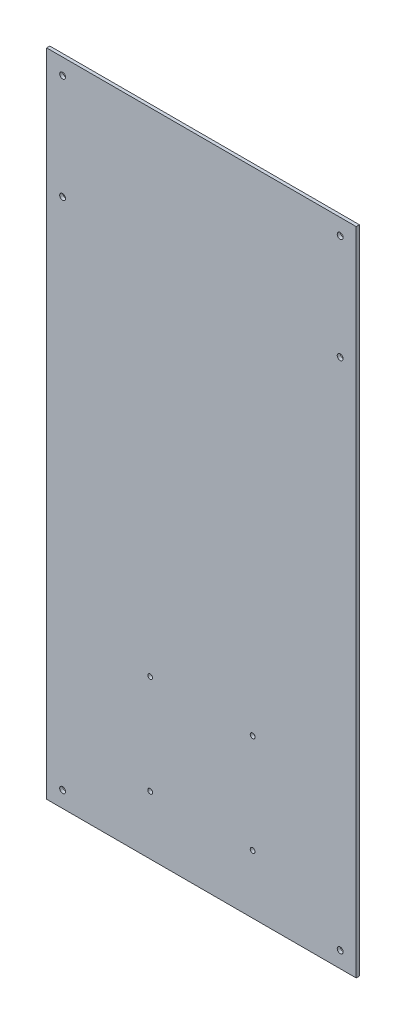
SolidWorks part; units mm, degrees
material "Acrylic (Medium-high impact)"
ref_plane "Front Plane" through (0, 0, 0) normal (0, 0, 1) x (1, 0, 0)
ref_plane "Top Plane" through (0, 0, 0) normal (0, 1, 0) x (1, 0, 0)
ref_plane "Right Plane" through (0, 0, 0) normal (1, 0, 0) x (0, 0, -1)
sketch "Sketch1" plane through (0, 0, 0) normal (0, 0, 1) x (1, 0, 0)
  line L0 (55, 0) -> (-55, 0) construction
  line L1 (-145, 304.8) -> (145, 304.8)
  line L2 (-145, 304.8) -> (-145, -304.8)
  line L3 (-145, -304.8) -> (145, -304.8)
  line L4 (145, 304.8) -> (145, -304.8)
  line L5 (-145, 304.8) -> (145, -304.8) construction
  line L6 (-145, -304.8) -> (145, 304.8) construction
  line L7 (48, -156.8) -> (-48, -249.8) construction
  line L8 (-48, -249.8) -> (48, -249.8) construction
  line L9 (48, -249.8) -> (48, -156.8) construction
  line L10 (48, -156.8) -> (-48, -156.8) construction
  line L11 (-48, -156.8) -> (-48, -249.8) construction
  line L12 (-48, -156.8) -> (48, -249.8) construction
  point P0 (0, 0)
  point P5 (-129.995, 289.795)
  point P6 (129.995, 289.795)
  point P7 (-48, -249.8)
  point P9 (-48, -156.8)
  point P10 (48, -156.8)
  point P11 (48, -249.8)
  point P12 (0, -203.3)
  point P16 (129.995, -289.795)
  point P17 (-129.995, -289.795)
  point P21 (-129.995, 191.395)
  point P22 (129.995, 191.395)
  point P23 (0, 0)
  point P24 (0, 0)
  point P25 (129.995, 191.395)
  point P26 (0, 0)
  point P27 (0, 0)
  dimension "D1" = 609.6
  dimension "D2" = 290
  dimension "D3" = 15.005
  dimension "D4" = 15.005
  dimension "D5" = 15.005
  dimension "D6" = 93
  dimension "D7" = 96
  dimension "D8" = 55
  dimension "D9" = 98.4
extrude "Boss-Extrude1" add sketch "Sketch1" along normal blind 3
hole_wizard "M5 Clearance Hole1" positions "Sketch2" profile "Sketch3" hole size "M5" standard "ANSI Metric" end condition through all
sketch "Sketch2" plane through (0, 0, 3) normal (0, 0, 1) x (1, 0, 0)
  point P0 (129.995, 289.795)
  point P3 (-129.995, 289.795)
  point P6 (-129.995, -289.795)
  point P9 (129.995, -289.795)
  point P12 (129.995, 191.395)
  point P15 (-129.995, 191.395)
sketch "Sketch3" plane through (129.995, 289.795, 3) normal (1, 0, 0) x (0, -1, 0)
  line L0 (0, 0) -> (0, 3)
  line L1 (0, 3) -> (2.75, 3)
  line L2 (2.75, 3) -> (2.75, 0)
  line L5 (2.75, 0) -> (0, 0)
  line L11 (0, -6.35) -> (0, 107.95) construction
  dimension "Thru Hole Dia." = 5.5
  dimension "Thru Hole Depth" = 3
hole_wizard "M4 Clearance Hole1" positions "Sketch4" profile "Sketch5" hole size "M4" standard "ANSI Metric" end condition through all
sketch "Sketch4" plane through (0, 0, 3) normal (0, 0, 1) x (1, 0, 0)
  point P0 (-48, -156.8)
  point P3 (-48, -249.8)
  point P6 (48, -249.8)
  point P9 (48, -156.8)
sketch "Sketch5" plane through (-48, -156.8, 3) normal (1, 0, 0) x (0, -1, 0)
  line L0 (0, 0) -> (0, 3)
  line L1 (0, 3) -> (2.25, 3)
  line L2 (2.25, 3) -> (2.25, 0)
  line L5 (2.25, 0) -> (0, 0)
  line L11 (0, -6.35) -> (0, 107.95) construction
  dimension "Thru Hole Dia." = 4.5
  dimension "Thru Hole Depth" = 3
